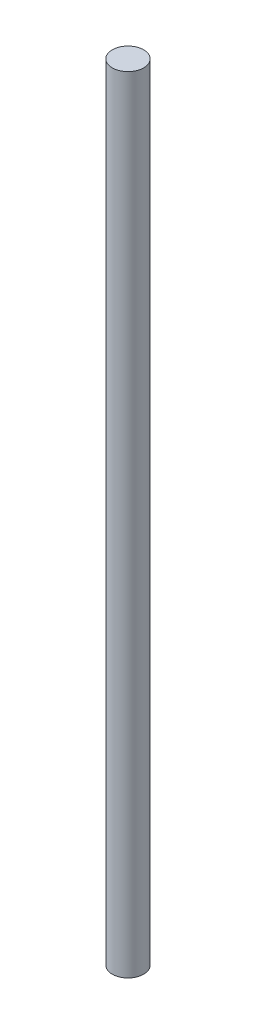
SolidWorks part; units mm, degrees
ref_plane "Front Plane" through (0, 0, 0) normal (0, 0, 1) x (1, 0, 0)
ref_plane "Top Plane" through (0, 0, 0) normal (0, 1, 0) x (1, 0, 0)
ref_plane "Right Plane" through (0, 0, 0) normal (1, 0, 0) x (0, 0, -1)
sketch "Sketch1" plane through (0, 0, 0) normal (0, 1, 0) x (1, 0, 0)
  circle A0 centre (0, 0) radius 5
extrude "Boss-Extrude1" add sketch "Sketch1" along normal blind 250
